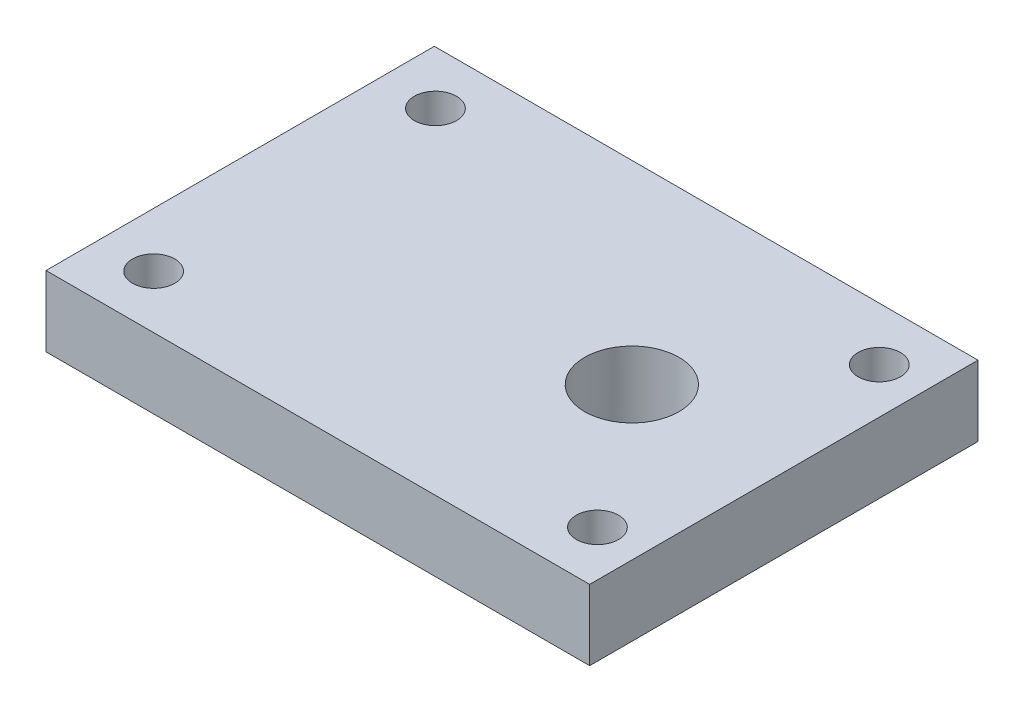
SolidWorks part; units mm, degrees
ref_plane "Front Plane" through (0, 0, 0) normal (0, 0, 1) x (1, 0, 0)
ref_plane "Top Plane" through (0, 0, 0) normal (0, 1, 0) x (1, 0, 0)
ref_plane "Right Plane" through (0, 0, 0) normal (1, 0, 0) x (0, 0, -1)
sketch "Sketch1" plane through (0, 0, 0) normal (0, 1, 0) x (1, 0, 0)
  line L1 (-24.5, -17.5) -> (24.5, -17.5)
  line L2 (-24.5, -17.5) -> (-24.5, 17.5)
  line L3 (-24.5, 17.5) -> (24.5, 17.5)
  line L4 (24.5, -17.5) -> (24.5, 17.5)
  line L5 (-24.5, -17.5) -> (24.5, 17.5) construction
  line L6 (-24.5, 17.5) -> (24.5, -17.5) construction
  circle A0 centre (-19.6, 12.7) radius 1.905
  circle A1 centre (20.4, 12.7) radius 1.905
  circle A2 centre (-19.6, -12.7) radius 1.905
  circle A3 centre (20.4, -12.7) radius 1.905
  point P0 (0, 0)
  point P12 (-14.5338, -10.5407)
  point P15 (14.0926, -8.028)
  dimension "D4" = 3.81
  dimension "D5" = 3.81
  dimension "D9" = 3.81
  dimension "D10" = 3.81
  dimension "D1" = 49
  dimension "D2" = 35
  dimension "D3" = 4.8
  dimension "D6" = 4.9
  dimension "D7" = 4.8
  dimension "D8" = 4.1
  dimension "D11" = 4.9
  dimension "D12" = 4.8
  dimension "D13" = 4.1
  dimension "D14" = 4.8
extrude "Boss-Extrude1" add sketch "Sketch1" along normal blind 6.35
sketch "Sketch2" plane through (0, 6.35, 0) normal (0, 1, 0) x (1, 0, 0)
  line L0 (-24.5, -17.5) -> (24.5, -17.5) construction
  line L2 (-24.5, 17.5) -> (-24.5, -17.5) construction
  circle A0 centre (10.8, 0) radius 4.25
  dimension "D1" = 8.5
  dimension "D2" = 17.5
  dimension "D3" = 35.3
extrude "Cut-Extrude1" cut sketch "Sketch2" against normal up to surface (6.35 mm away) up to face at (20.4, 0, 14.605)
